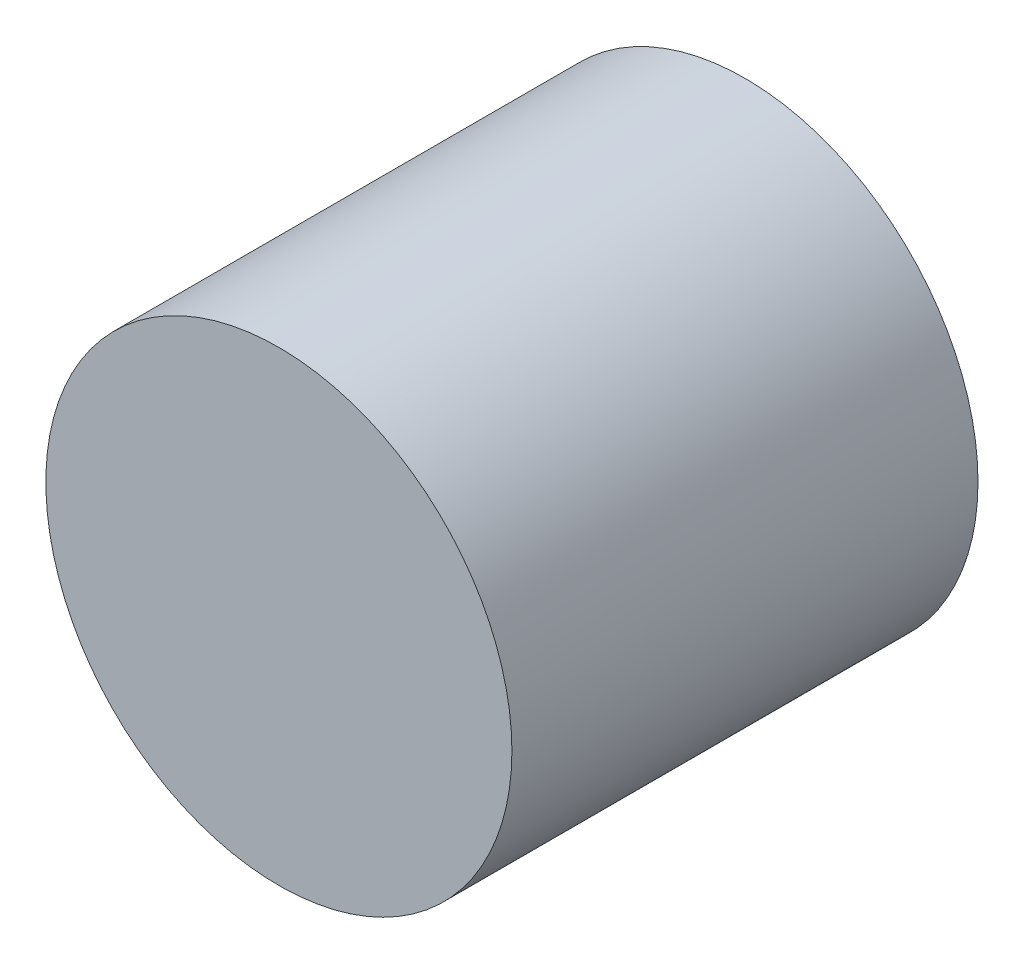
SolidWorks part; units mm, degrees
ref_plane "前视基准面" through (0, 0, 0) normal (0, 0, 1) x (1, 0, 0)
ref_plane "上视基准面" through (0, 0, 0) normal (0, 1, 0) x (1, 0, 0)
ref_plane "右视基准面" through (0, 0, 0) normal (1, 0, 0) x (0, 0, -1)
sketch "草图1" plane through (0, 0, 0) normal (0, 0, 1) x (1, 0, 0)
  circle A0 centre (0, 0) radius 0.5
extrude "凸台-拉伸1" add sketch "草图1" along normal blind 1 contours A0
